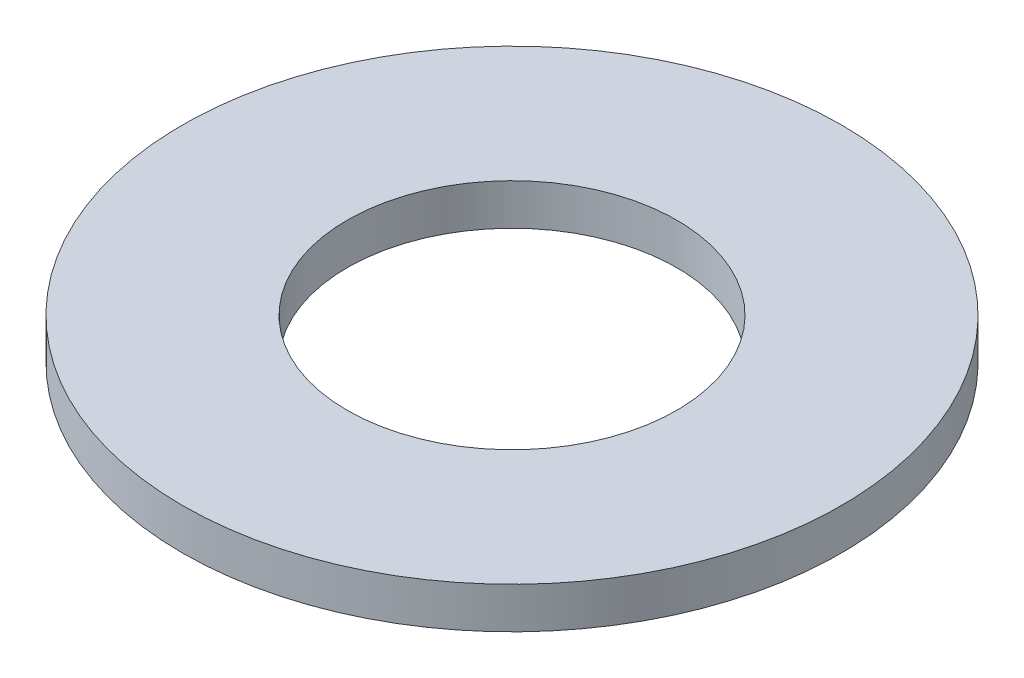
SolidWorks part; units mm, degrees
ref_plane "Front Plane" through (0, 0, 0) normal (0, 0, 1) x (1, 0, 0)
ref_plane "Top Plane" through (0, 0, 0) normal (0, 1, 0) x (1, 0, 0)
ref_plane "Right Plane" through (0, 0, 0) normal (1, 0, 0) x (0, 0, -1)
sketch "Sketch1" plane through (0, 0, 0) normal (0, 1, 0) x (1, 0, 0)
  circle A0 centre (0, 0) radius 6.35
  circle A1 centre (0, 0) radius 3.175
  dimension "D1" = 6.35
  dimension "D2" = 12.7
extrude "Boss-Extrude1" add sketch "Sketch1" along normal blind 0.7937
